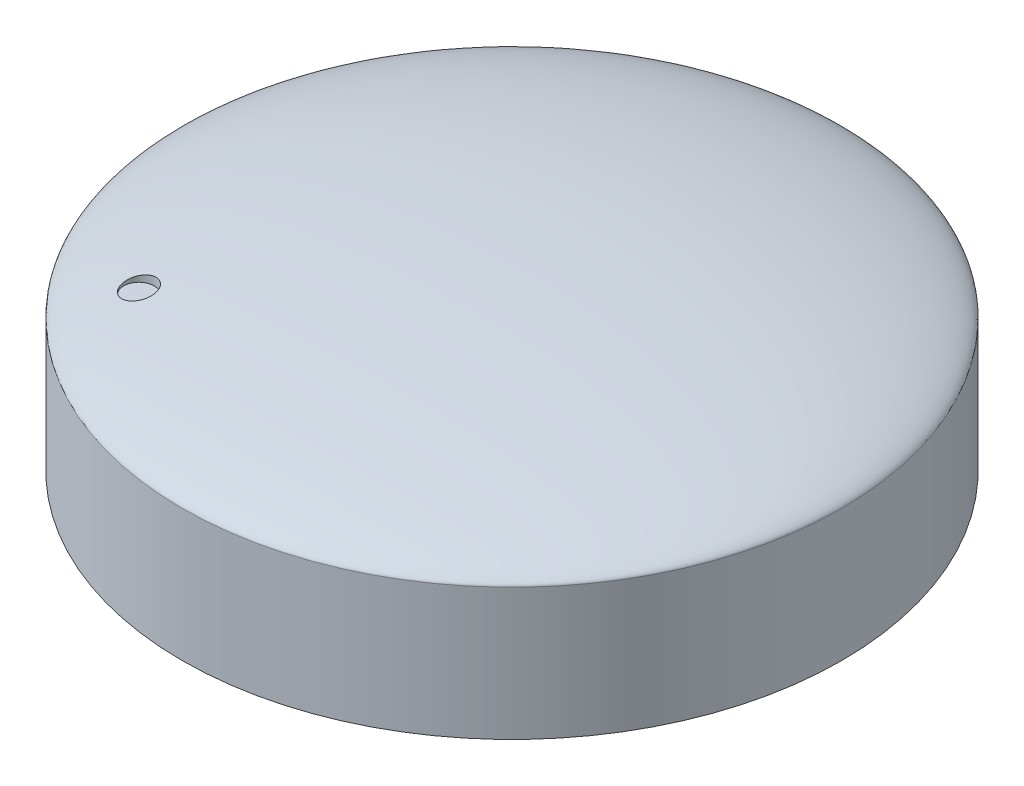
SolidWorks part; units mm, degrees
material "Hêtre"
ref_plane "Plan de face" through (0, 0, 0) normal (0, 0, 1) x (1, 0, 0)
ref_plane "Plan de dessus" through (0, 0, 0) normal (0, 1, 0) x (1, 0, 0)
ref_plane "Plan de droite" through (0, 0, 0) normal (1, 0, 0) x (0, 0, -1)
ref_plane "Plan tout dessus" through (0, 18, 0) normal (0, 1, 0) x (1, 0, 0)
sketch "Esquisse1" plane through (0, 0, 0) normal (0, 1, 0) x (1, 0, 0)
  circle A0 centre (0, 0) radius 32.5
  dimension "D1" = 65
extrude "Boss.-Extru.1" add sketch "Esquisse1" along normal blind 18 contours A0
sketch "Esquisse2" plane through (0, 0, 0) normal (0, 0, 1) x (1, 0, 0)
  line L0 (-32.5, 18) -> (-32.5, 0) construction
  line L1 (-32.5, 13) -> (-32.5, 19)
  line L2 (-32.5, 19) -> (0, 19)
  line L3 (0, 19) -> (0, 18)
  line L4 (0, 0) -> (0, 27.0493) construction
  line L5 (32.5, 18) -> (-32.5, 18) construction
  line L6 (-32.5, 15.4465) -> (-32.5, 8.7782) construction
  line L7 (17.2644, 18) -> (-17.2979, 18) construction
  spline S0 degree 3 poles (-32.5, 13) (-32.5, 14.1723) (-21.6014, 18) (0, 18) knots 0 0 0 0 1 1 1 1
  dimension "D1" = 5
  dimension "D2" = 1
revolve "Enlèvement de matière-Révolution1" cut sketch "Esquisse2" angle 360 about L4
sketch "Esquisse3" plane through (0, 18, 0) normal (0, 1, 0) x (1, 0, 0)
  line L0 (0, 0) -> (0, -35.0028) construction
  line L1 (-18.3848, -18.3848) -> (0, 0) construction
  circle A0 centre (-18.3848, -18.3848) radius 1.5
  circle A1 centre (0, 0) radius 32.5 construction
  dimension "D1" = 3
  dimension "D2" = 26
  dimension "D3" = 45
extrude "Enlèv. mat.-Extru.1" cut sketch "Esquisse3" against normal blind 3
sketch "Esquisse4" plane through (0, 0, 0) normal (0, 1, 0) x (1, 0, 0)
  circle A0 centre (0, 0) radius 14.75
  dimension "D1" = 29.5
extrude "Boss.-Extru.3" add sketch "Esquisse4" against normal blind 12
